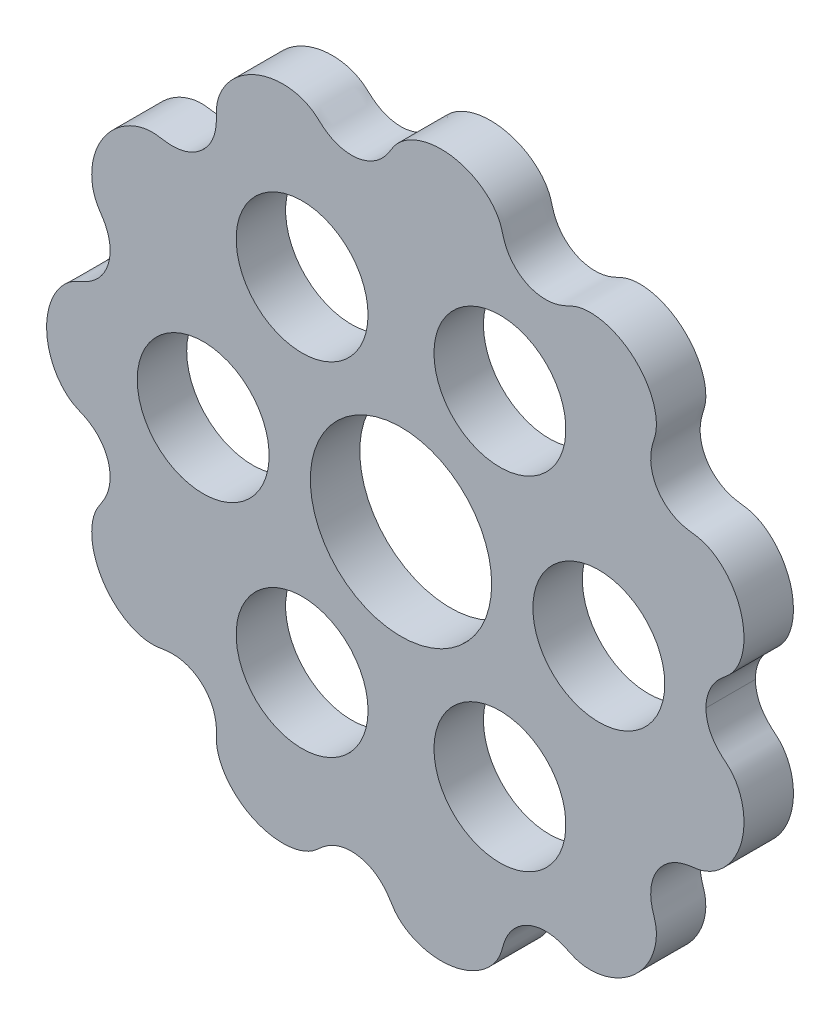
SolidWorks part; units mm, degrees
ref_plane "Front Plane" through (0, 0, 0) normal (0, 0, 1) x (1, 0, 0)
ref_plane "Top Plane" through (0, 0, 0) normal (0, 1, 0) x (1, 0, 0)
ref_plane "Right Plane" through (0, 0, 0) normal (1, 0, 0) x (0, 0, -1)
sketch "Sketch1" plane through (0, 0, 0) normal (0, 0, 1) x (1, 0, 0)
  circle A0 centre (0, 0) radius 50
  dimension "D1" = 100
extrude "Boss-Extrude1" add sketch "Sketch1" against normal blind 6
sketch "Sketch4" plane through (0, 0, 0) normal (0, 0, 1) x (1, 0, 0)
  line L1 (-43, 0) -> (37, 0) construction
  circle A0 centre (0, 0) radius 50
  circle A1 centre (0, 0) radius 50 construction
  spline S0 degree 4 poles (41.5851, 10.3346) (41.6199, 9.8835) (41.6243, 9.2034) (41.5317, 8.2988) (41.2403, 7.1964) (40.9372, 6.4519) (40.6006, 5.8458) (40.2846, 5.4003) (40.0318, 5.099) (39.7825, 4.8438) (39.5448, 4.6291) (39.2991, 4.4237) (39.054, 4.2176) (38.7552, 3.9511) (38.446, 3.6423) (38.1379, 3.2825) (37.8433, 2.8662) (37.6072, 2.4641) (37.4069, 2.043) (37.2646, 1.6607) (37.1673, 1.3249) (37.1028, 1.0413) (37.0614, 0.8113) (37.0342, 0.6103) (37.0173, 0.4389) (37.0076, 0.2873) (37.0024, 0.1621) (36.9997, 0.0436) (36.9998, -0.0533) (37.0029, -0.1805) (37.0092, -0.3185) (37.021, -0.4826) (37.0414, -0.6698) (37.0837, -0.9559) (37.1649, -1.3314) (37.2949, -1.7606) (37.4902, -2.2338) (37.7296, -2.6858) (38.0102, -3.1128) (38.3023, -3.4793) (38.5927, -3.7913) (38.8708, -4.0561) (39.128, -4.2811) (39.3908, -4.4995) (39.6509, -4.7212) (39.96, -5.0164) (40.2952, -5.4031) (40.633, -5.894) (40.9508, -6.4943) (41.2036, -7.1227) (41.4194, -7.8549) (41.5727, -8.6911) (41.636, -9.6259) (41.5806, -10.6475) (41.4043, -11.6601) (41.1093, -12.6496) (40.6979, -13.602) (40.1724, -14.5022) (39.4909, -15.3931) (38.7523, -16.1139) (37.9929, -16.6697) (37.2409, -17.0709) (36.6814, -17.2882) (36.1812, -17.4183) (35.7535, -17.4878) (35.4097, -17.5305) (35.0662, -17.5753) (34.7244, -17.6334) (33.9621, -17.799) (32.8171, -18.2368) (31.6914, -19.0898) (30.8224, -20.3839) (30.408, -21.5834) (30.2645, -22.5652) (30.2961, -23.3919) (30.4095, -24.0426) (30.5337, -24.523) (30.6289, -24.842) (30.7295, -25.1591) (30.8226, -25.4788) (30.9148, -25.8847) (30.9808, -26.383) (30.9944, -26.9717) (30.9331, -27.6434) (30.8023, -28.3074) (30.5866, -29.0299) (30.2677, -29.7983) (29.7091, -30.8112) (28.7943, -31.9885) (27.6691, -32.9783) (26.3797, -33.7385) (25.287, -34.1684) (24.4667, -34.3895) (23.7014, -34.5114) (23.0895, -34.5479) (22.5645, -34.5327) (22.0494, -34.4779) (21.6292, -34.3987) (21.2207, -34.2838) (20.8282, -34.133) (20.5223, -33.9937) (20.2197, -33.8474) (19.9143, -33.7068) (19.4515, -33.5146) (18.8164, -33.31) (17.9928, -33.1639) (16.9896, -33.1739) (15.7388, -33.4271) (14.34, -34.1197) (13.2844, -35.1853) (12.6832, -36.3498) (12.4167, -37.1715) (12.3007, -37.5873) (12.2097, -37.9202) (12.077, -38.3311) (11.8737, -38.8043) (11.5763, -39.3231) (11.0699, -40.0048) (10.2279, -40.8568) (8.9477, -41.7397) (7.1761, -42.4496) (5.3677, -42.7131) (3.8099, -42.6315) (2.6321, -42.3721) (1.8212, -42.0927) (1.1256, -41.7663) (0.541, -41.4194) (-0.0018, -41.0141) (-0.4313, -40.6073) (-0.7569, -40.2215) (-0.9962, -39.8786) (-1.1736, -39.5952) (-1.3489, -39.3105) (-1.532, -39.0307) (-1.8282, -38.6168) (-2.2737, -38.0967) (-2.9231, -37.5266) (-3.823, -37.0029) (-4.8035, -36.6676) (-5.8255, -36.5318) (-6.847, -36.5969) (-7.83, -36.8545) (-8.5941, -37.2186) (-9.1572, -37.5904) (-9.554, -37.904) (-9.8106, -38.1246) (-10.0615, -38.3513) (-10.3155, -38.5748) (-10.6482, -38.8362) (-11.0061, -39.0672) (-11.3852, -39.2662) (-11.8611, -39.4687) (-12.356, -39.6355) (-12.9486, -39.778) (-13.7162, -39.8842) (-14.5693, -39.9112) (-15.7506, -39.8147) (-17.2442, -39.4469) (-18.8902, -38.6799) (-20.382, -37.4935) (-21.3601, -36.2698) (-21.9217, -35.202) (-22.1788, -34.4781) (-22.3014, -33.9783) (-22.3596, -33.5951) (-22.3833, -33.3352) (-22.3952, -33.0746) (-22.3968, -32.8138) (-22.3902, -32.5096) (-22.3873, -32.1618) (-22.3978, -31.8141) (-22.4393, -31.2937) (-22.5601, -30.6065) (-22.9189, -29.5253) (-23.6399, -28.4298) (-24.6121, -27.5729) (-25.7462, -27.0054) (-26.6974, -26.7348) (-27.5181, -26.6568) (-28.1758, -26.6819) (-28.6667, -26.7394) (-28.9944, -26.7893) (-29.3213, -26.8434) (-29.6498, -26.8877) (-30.0633, -26.9174) (-30.5638, -26.9075) (-31.1457, -26.8334) (-31.7983, -26.674) (-32.4334, -26.4476) (-33.114, -26.1295) (-33.825, -25.7034) (-34.7425, -25.0061) (-35.7753, -23.9302) (-36.5936, -22.6707) (-37.1604, -21.2783) (-37.4266, -20.1279) (-37.5242, -19.283) (-37.5315, -18.511) (-37.4781, -17.9059) (-37.3867, -17.3936) (-37.2577, -16.8948) (-37.1182, -16.4917) (-36.9445, -16.1045) (-36.737, -15.7376) (-36.5542, -15.4544) (-36.3659, -15.175) (-36.1835, -14.8916) (-35.9275, -14.4575) (-35.6356, -13.852) (-35.3771, -13.0493) (-35.2517, -12.0445) (-35.3352, -10.8098) (-35.7196, -9.6388) (-36.3073, -8.7132) (-36.9724, -8.0325) (-37.4669, -7.6315) (-37.8668, -7.3655) (-38.2534, -7.1506) (-38.6177, -6.9754) (-38.9133, -6.8446) (-39.21, -6.7161) (-39.5023, -6.5777) (-39.8205, -6.4022) (-40.1575, -6.1807) (-40.6012, -5.8325) (-41.114, -5.3257) (-41.632, -4.6671) (-42.1172, -3.8458) (-42.4493, -3.0848) (-42.6697, -2.4088) (-42.7944, -1.8999) (-42.8599, -1.5689) (-42.9114, -1.2536) (-42.9441, -1.0039) (-42.9692, -0.7529) (-42.9848, -0.5312) (-42.9923, -0.3757) (-42.9975, -0.2143) (-43.0007, -0.0397) (-43.0003, 0.0847) (-42.9957, 0.293) (-42.9867, 0.4997) (-42.9737, 0.6941) (-42.9527, 0.9239) (-42.9207, 1.1877) (-42.8707, 1.5143) (-42.7946, 1.9043) (-42.6826, 2.3538) (-42.5224, 2.8587) (-42.3301, 3.3521) (-42.09, 3.8653) (-41.7941, 4.3914) (-41.4337, 4.9212) (-40.9994, 5.4418) (-40.511, 5.9138) (-40.0366, 6.2736) (-39.5966, 6.533) (-39.2118, 6.7155) (-38.8993, 6.8506) (-38.5101, 7.0233) (-37.9589, 7.3002) (-37.2793, 7.7414) (-36.7472, 8.2372) (-36.3985, 8.6664) (-36.2399, 8.8922) knots 0 0 0 0 0 0.010457 0.015686 0.020914 0.026295 0.028985 0.031675 0.033525 0.035376 0.037227 0.039077 0.040928 0.042779 0.04648 0.049171 0.051863 0.054554 0.057246 0.059937 0.061283 0.062628 0.063974 0.065319 0.065992 0.066665 0.067338 0.06801 0.06875 0.069491 0.070231 0.070971 0.072451 0.073931 0.076891 0.079851 0.082799 0.085748 0.088696 0.091645 0.09362 0.095594 0.097569 0.099544 0.101519 0.103494 0.107443 0.111351 0.115259 0.119167 0.123074 0.128973 0.134872 0.140771 0.146669 0.152679 0.158688 0.164698 0.170707 0.178536 0.182451 0.186366 0.19037 0.192373 0.194375 0.196377 0.198379 0.200382 0.202384 0.214412 0.226466 0.232173 0.237879 0.243576 0.249273 0.251196 0.253119 0.255043 0.256966 0.258889 0.260813 0.264659 0.268564 0.272469 0.276374 0.280279 0.285972 0.291665 0.30305 0.314568 0.320327 0.326086 0.330128 0.33417 0.338213 0.340234 0.342255 0.34614 0.348082 0.350025 0.351967 0.35391 0.355852 0.357795 0.36355 0.369305 0.37508 0.380855 0.392868 0.404851 0.408842 0.410837 0.412832 0.414827 0.416822 0.420812 0.424713 0.428614 0.436416 0.448392 0.460368 0.472309 0.47828 0.484251 0.488173 0.492095 0.496017 0.499939 0.503803 0.505735 0.507667 0.509599 0.511531 0.513463 0.515395 0.521361 0.527327 0.533319 0.539312 0.54516 0.551008 0.556835 0.562661 0.564616 0.566571 0.568526 0.57048 0.572435 0.57439 0.5783 0.580309 0.582319 0.586338 0.590358 0.594377 0.600204 0.606031 0.617686 0.629747 0.641809 0.649666 0.653594 0.657523 0.659533 0.661542 0.662547 0.663552 0.665562 0.667571 0.669581 0.671591 0.673601 0.679635 0.685669 0.697766 0.703453 0.709139 0.714817 0.720495 0.72241 0.724326 0.726241 0.728156 0.730071 0.731987 0.735817 0.739708 0.743598 0.747489 0.751379 0.757051 0.762723 0.774066 0.785679 0.791485 0.797291 0.801296 0.805301 0.809306 0.811308 0.813311 0.817206 0.819153 0.8211 0.823048 0.824995 0.826943 0.82889 0.834696 0.840502 0.846329 0.852156 0.863131 0.868612 0.871353 0.874093 0.87783 0.879699 0.881567 0.883436 0.885304 0.887173 0.889041 0.891829 0.894617 0.900194 0.905666 0.911137 0.916609 0.919345 0.922081 0.923244 0.924407 0.926733 0.927896 0.929058 0.92964 0.930221 0.931384 0.932914 0.933678 0.934443 0.935973 0.937502 0.939031 0.940561 0.94362 0.946678 0.949737 0.952796 0.955855 0.959766 0.963677 0.967588 0.971499 0.975435 0.977403 0.979372 0.98134 0.983308 0.987244 0.993622 1 1 1 1 1 construction
  spline S1 degree 4 poles (37, 0) (37, -0.0276) (37.0005, -0.0829) (37.0029, -0.1805) (37.0092, -0.3185) (37.021, -0.4826) (37.0414, -0.6698) (37.0837, -0.9559) (37.1649, -1.3314) (37.2949, -1.7606) (37.4902, -2.2338) (37.7296, -2.6858) (38.0102, -3.1128) (38.3023, -3.4793) (38.5927, -3.7913) (38.8708, -4.0561) (39.128, -4.2811) (39.3908, -4.4995) (39.6509, -4.7212) (39.96, -5.0164) (40.2952, -5.4031) (40.633, -5.894) (40.9508, -6.4943) (41.2036, -7.1227) (41.4194, -7.8549) (41.5727, -8.6911) (41.636, -9.6259) (41.5806, -10.6475) (41.4043, -11.6601) (41.1093, -12.6496) (40.6979, -13.602) (40.1724, -14.5022) (39.4909, -15.3931) (38.7523, -16.1139) (37.9929, -16.6697) (37.2409, -17.0709) (36.6814, -17.2882) (36.1812, -17.4183) (35.7535, -17.4878) (35.4097, -17.5305) (35.0662, -17.5753) (34.7244, -17.6334) (33.9621, -17.799) (32.8171, -18.2368) (31.6914, -19.0898) (30.8224, -20.3839) (30.408, -21.5834) (30.2645, -22.5652) (30.2961, -23.3919) (30.4095, -24.0426) (30.5337, -24.523) (30.6289, -24.842) (30.7295, -25.1591) (30.8226, -25.4788) (30.9148, -25.8847) (30.9808, -26.383) (30.9944, -26.9717) (30.9331, -27.6434) (30.8023, -28.3074) (30.5866, -29.0299) (30.2677, -29.7983) (29.7091, -30.8112) (28.7943, -31.9885) (27.6691, -32.9783) (26.3797, -33.7385) (25.287, -34.1684) (24.4667, -34.3895) (23.7014, -34.5114) (23.0895, -34.5479) (22.5645, -34.5327) (22.0494, -34.4779) (21.6292, -34.3987) (21.2207, -34.2838) (20.8282, -34.133) (20.5223, -33.9937) (20.2197, -33.8474) (19.9143, -33.7068) (19.4515, -33.5146) (18.8164, -33.31) (17.9928, -33.1639) (16.9896, -33.1739) (15.7388, -33.4271) (14.34, -34.1197) (13.2844, -35.1853) (12.6832, -36.3498) (12.4167, -37.1715) (12.3007, -37.5873) (12.2097, -37.9202) (12.077, -38.3311) (11.8737, -38.8043) (11.5763, -39.3231) (11.0699, -40.0048) (10.2279, -40.8568) (8.9477, -41.7397) (7.1761, -42.4496) (5.3677, -42.7131) (3.8099, -42.6315) (2.6321, -42.3721) (1.8212, -42.0927) (1.1256, -41.7663) (0.541, -41.4194) (-0.0018, -41.0141) (-0.4313, -40.6073) (-0.7569, -40.2215) (-0.9962, -39.8786) (-1.1736, -39.5952) (-1.3489, -39.3105) (-1.532, -39.0307) (-1.8282, -38.6168) (-2.2737, -38.0967) (-2.9231, -37.5266) (-3.823, -37.0029) (-4.8035, -36.6676) (-5.8255, -36.5318) (-6.847, -36.5969) (-7.83, -36.8545) (-8.5941, -37.2186) (-9.1572, -37.5904) (-9.554, -37.904) (-9.8106, -38.1246) (-10.0615, -38.3513) (-10.3155, -38.5748) (-10.6482, -38.8362) (-11.0061, -39.0672) (-11.3852, -39.2662) (-11.8611, -39.4687) (-12.356, -39.6355) (-12.9486, -39.778) (-13.7162, -39.8842) (-14.5693, -39.9112) (-15.7506, -39.8147) (-17.2442, -39.4469) (-18.8902, -38.6799) (-20.382, -37.4935) (-21.3601, -36.2698) (-21.9217, -35.202) (-22.1788, -34.4781) (-22.3014, -33.9783) (-22.3596, -33.5951) (-22.3833, -33.3352) (-22.3952, -33.0746) (-22.3968, -32.8138) (-22.3902, -32.5096) (-22.3873, -32.1618) (-22.3978, -31.8141) (-22.4393, -31.2937) (-22.5601, -30.6065) (-22.9189, -29.5253) (-23.6399, -28.4298) (-24.6121, -27.5729) (-25.7462, -27.0054) (-26.6974, -26.7348) (-27.5181, -26.6568) (-28.1758, -26.6819) (-28.6667, -26.7394) (-28.9944, -26.7893) (-29.3213, -26.8434) (-29.6498, -26.8877) (-30.0633, -26.9174) (-30.5638, -26.9075) (-31.1457, -26.8334) (-31.7983, -26.674) (-32.4334, -26.4476) (-33.114, -26.1295) (-33.825, -25.7034) (-34.7425, -25.0061) (-35.7753, -23.9302) (-36.5936, -22.6707) (-37.1604, -21.2783) (-37.4266, -20.1279) (-37.5242, -19.283) (-37.5315, -18.511) (-37.4781, -17.9059) (-37.3867, -17.3936) (-37.2577, -16.8948) (-37.1182, -16.4917) (-36.9445, -16.1045) (-36.737, -15.7376) (-36.5542, -15.4544) (-36.3659, -15.175) (-36.1835, -14.8916) (-35.9275, -14.4575) (-35.6356, -13.852) (-35.3771, -13.0493) (-35.2517, -12.0445) (-35.3352, -10.8098) (-35.7196, -9.6388) (-36.3073, -8.7132) (-36.9724, -8.0325) (-37.4669, -7.6315) (-37.8668, -7.3655) (-38.2534, -7.1506) (-38.6177, -6.9754) (-38.9133, -6.8446) (-39.21, -6.7161) (-39.5023, -6.5777) (-39.8205, -6.4022) (-40.1575, -6.1807) (-40.6012, -5.8325) (-41.114, -5.3257) (-41.632, -4.6671) (-42.1172, -3.8458) (-42.4493, -3.0848) (-42.6697, -2.4088) (-42.7944, -1.8999) (-42.8599, -1.5689) (-42.9114, -1.2536) (-42.9441, -1.0039) (-42.9692, -0.7529) (-42.9848, -0.5312) (-42.9923, -0.3757) (-42.9975, -0.2143) (-42.9994, -0.109) (-43, -0.0434) (-43, 0) knots 0.06801 0.06801 0.06801 0.06801 0.06801 0.06875 0.069491 0.070231 0.070971 0.072451 0.073931 0.076891 0.079851 0.082799 0.085748 0.088696 0.091645 0.09362 0.095594 0.097569 0.099544 0.101519 0.103494 0.107443 0.111351 0.115259 0.119167 0.123074 0.128973 0.134872 0.140771 0.146669 0.152679 0.158688 0.164698 0.170707 0.178536 0.182451 0.186366 0.19037 0.192373 0.194375 0.196377 0.198379 0.200382 0.202384 0.214412 0.226466 0.232173 0.237879 0.243576 0.249273 0.251196 0.253119 0.255043 0.256966 0.258889 0.260813 0.264659 0.268564 0.272469 0.276374 0.280279 0.285972 0.291665 0.30305 0.314568 0.320327 0.326086 0.330128 0.33417 0.338213 0.340234 0.342255 0.34614 0.348082 0.350025 0.351967 0.35391 0.355852 0.357795 0.36355 0.369305 0.37508 0.380855 0.392868 0.404851 0.408842 0.410837 0.412832 0.414827 0.416822 0.420812 0.424713 0.428614 0.436416 0.448392 0.460368 0.472309 0.47828 0.484251 0.488173 0.492095 0.496017 0.499939 0.503803 0.505735 0.507667 0.509599 0.511531 0.513463 0.515395 0.521361 0.527327 0.533319 0.539312 0.54516 0.551008 0.556835 0.562661 0.564616 0.566571 0.568526 0.57048 0.572435 0.57439 0.5783 0.580309 0.582319 0.586338 0.590358 0.594377 0.600204 0.606031 0.617686 0.629747 0.641809 0.649666 0.653594 0.657523 0.659533 0.661542 0.662547 0.663552 0.665562 0.667571 0.669581 0.671591 0.673601 0.679635 0.685669 0.697766 0.703453 0.709139 0.714817 0.720495 0.72241 0.724326 0.726241 0.728156 0.730071 0.731987 0.735817 0.739708 0.743598 0.747489 0.751379 0.757051 0.762723 0.774066 0.785679 0.791485 0.797291 0.801296 0.805301 0.809306 0.811308 0.813311 0.817206 0.819153 0.8211 0.823048 0.824995 0.826943 0.82889 0.834696 0.840502 0.846329 0.852156 0.863131 0.868612 0.871353 0.874093 0.87783 0.879699 0.881567 0.883436 0.885304 0.887173 0.889041 0.891829 0.894617 0.900194 0.905666 0.911137 0.916609 0.919345 0.922081 0.923244 0.924407 0.926733 0.927896 0.929058 0.92964 0.930221 0.931384 0.931384 0.931384 0.931384 0.931384
  spline S2 degree 4 poles (37, 0) (37, 0.0276) (37.0005, 0.0829) (37.0029, 0.1805) (37.0092, 0.3185) (37.021, 0.4826) (37.0414, 0.6698) (37.0837, 0.9559) (37.1649, 1.3314) (37.2949, 1.7606) (37.4902, 2.2338) (37.7296, 2.6858) (38.0102, 3.1128) (38.3023, 3.4793) (38.5927, 3.7913) (38.8708, 4.0561) (39.128, 4.2811) (39.3908, 4.4995) (39.6509, 4.7212) (39.96, 5.0164) (40.2952, 5.4031) (40.633, 5.894) (40.9508, 6.4943) (41.2036, 7.1227) (41.4194, 7.8549) (41.5727, 8.6911) (41.636, 9.6259) (41.5806, 10.6475) (41.4043, 11.6601) (41.1093, 12.6496) (40.6979, 13.602) (40.1724, 14.5022) (39.4909, 15.3931) (38.7523, 16.1139) (37.9929, 16.6697) (37.2409, 17.0709) (36.6814, 17.2882) (36.1812, 17.4183) (35.7535, 17.4878) (35.4097, 17.5305) (35.0662, 17.5753) (34.7244, 17.6334) (33.9621, 17.799) (32.8171, 18.2368) (31.6914, 19.0898) (30.8224, 20.3839) (30.408, 21.5834) (30.2645, 22.5652) (30.2961, 23.3919) (30.4095, 24.0426) (30.5337, 24.523) (30.6289, 24.842) (30.7295, 25.1591) (30.8226, 25.4788) (30.9148, 25.8847) (30.9808, 26.383) (30.9944, 26.9717) (30.9331, 27.6434) (30.8023, 28.3074) (30.5866, 29.0299) (30.2677, 29.7983) (29.7091, 30.8112) (28.7943, 31.9885) (27.6691, 32.9783) (26.3797, 33.7385) (25.287, 34.1684) (24.4667, 34.3895) (23.7014, 34.5114) (23.0895, 34.5479) (22.5645, 34.5327) (22.0494, 34.4779) (21.6292, 34.3987) (21.2207, 34.2838) (20.8282, 34.133) (20.5223, 33.9937) (20.2197, 33.8474) (19.9143, 33.7068) (19.4515, 33.5146) (18.8164, 33.31) (17.9928, 33.1639) (16.9896, 33.1739) (15.7388, 33.4271) (14.34, 34.1197) (13.2844, 35.1853) (12.6832, 36.3498) (12.4167, 37.1715) (12.3007, 37.5873) (12.2097, 37.9202) (12.077, 38.3311) (11.8737, 38.8043) (11.5763, 39.3231) (11.0699, 40.0048) (10.2279, 40.8568) (8.9477, 41.7397) (7.1761, 42.4496) (5.3677, 42.7131) (3.8099, 42.6315) (2.6321, 42.3721) (1.8212, 42.0927) (1.1256, 41.7663) (0.541, 41.4194) (-0.0018, 41.0141) (-0.4313, 40.6073) (-0.7569, 40.2215) (-0.9962, 39.8786) (-1.1736, 39.5952) (-1.3489, 39.3105) (-1.532, 39.0307) (-1.8282, 38.6168) (-2.2737, 38.0967) (-2.9231, 37.5266) (-3.823, 37.0029) (-4.8035, 36.6676) (-5.8255, 36.5318) (-6.847, 36.5969) (-7.83, 36.8545) (-8.5941, 37.2186) (-9.1572, 37.5904) (-9.554, 37.904) (-9.8106, 38.1246) (-10.0615, 38.3513) (-10.3155, 38.5748) (-10.6482, 38.8362) (-11.0061, 39.0672) (-11.3852, 39.2662) (-11.8611, 39.4687) (-12.356, 39.6355) (-12.9486, 39.778) (-13.7162, 39.8842) (-14.5693, 39.9112) (-15.7506, 39.8147) (-17.2442, 39.4469) (-18.8902, 38.6799) (-20.382, 37.4935) (-21.3601, 36.2698) (-21.9217, 35.202) (-22.1788, 34.4781) (-22.3014, 33.9783) (-22.3596, 33.5951) (-22.3833, 33.3352) (-22.3952, 33.0746) (-22.3968, 32.8138) (-22.3902, 32.5096) (-22.3873, 32.1618) (-22.3978, 31.8141) (-22.4393, 31.2937) (-22.5601, 30.6065) (-22.9189, 29.5253) (-23.6399, 28.4298) (-24.6121, 27.5729) (-25.7462, 27.0054) (-26.6974, 26.7348) (-27.5181, 26.6568) (-28.1758, 26.6819) (-28.6667, 26.7394) (-28.9944, 26.7893) (-29.3213, 26.8434) (-29.6498, 26.8877) (-30.0633, 26.9174) (-30.5638, 26.9075) (-31.1457, 26.8334) (-31.7983, 26.674) (-32.4334, 26.4476) (-33.114, 26.1295) (-33.825, 25.7034) (-34.7425, 25.0061) (-35.7753, 23.9302) (-36.5936, 22.6707) (-37.1604, 21.2783) (-37.4266, 20.1279) (-37.5242, 19.283) (-37.5315, 18.511) (-37.4781, 17.9059) (-37.3867, 17.3936) (-37.2577, 16.8948) (-37.1182, 16.4917) (-36.9445, 16.1045) (-36.737, 15.7376) (-36.5542, 15.4544) (-36.3659, 15.175) (-36.1835, 14.8916) (-35.9275, 14.4575) (-35.6356, 13.852) (-35.3771, 13.0493) (-35.2517, 12.0445) (-35.3352, 10.8098) (-35.7196, 9.6388) (-36.3073, 8.7132) (-36.9724, 8.0325) (-37.4669, 7.6315) (-37.8668, 7.3655) (-38.2534, 7.1506) (-38.6177, 6.9754) (-38.9133, 6.8446) (-39.21, 6.7161) (-39.5023, 6.5777) (-39.8205, 6.4022) (-40.1575, 6.1807) (-40.6012, 5.8325) (-41.114, 5.3257) (-41.632, 4.6671) (-42.1172, 3.8458) (-42.4493, 3.0848) (-42.6697, 2.4088) (-42.7944, 1.8999) (-42.8599, 1.5689) (-42.9114, 1.2536) (-42.9441, 1.0039) (-42.9692, 0.7529) (-42.9848, 0.5312) (-42.9923, 0.3757) (-42.9975, 0.2143) (-42.9994, 0.109) (-43, 0.0434) (-43, 0) knots 0.06801 0.06801 0.06801 0.06801 0.06801 0.06875 0.069491 0.070231 0.070971 0.072451 0.073931 0.076891 0.079851 0.082799 0.085748 0.088696 0.091645 0.09362 0.095594 0.097569 0.099544 0.101519 0.103494 0.107443 0.111351 0.115259 0.119167 0.123074 0.128973 0.134872 0.140771 0.146669 0.152679 0.158688 0.164698 0.170707 0.178536 0.182451 0.186366 0.19037 0.192373 0.194375 0.196377 0.198379 0.200382 0.202384 0.214412 0.226466 0.232173 0.237879 0.243576 0.249273 0.251196 0.253119 0.255043 0.256966 0.258889 0.260813 0.264659 0.268564 0.272469 0.276374 0.280279 0.285972 0.291665 0.30305 0.314568 0.320327 0.326086 0.330128 0.33417 0.338213 0.340234 0.342255 0.34614 0.348082 0.350025 0.351967 0.35391 0.355852 0.357795 0.36355 0.369305 0.37508 0.380855 0.392868 0.404851 0.408842 0.410837 0.412832 0.414827 0.416822 0.420812 0.424713 0.428614 0.436416 0.448392 0.460368 0.472309 0.47828 0.484251 0.488173 0.492095 0.496017 0.499939 0.503803 0.505735 0.507667 0.509599 0.511531 0.513463 0.515395 0.521361 0.527327 0.533319 0.539312 0.54516 0.551008 0.556835 0.562661 0.564616 0.566571 0.568526 0.57048 0.572435 0.57439 0.5783 0.580309 0.582319 0.586338 0.590358 0.594377 0.600204 0.606031 0.617686 0.629747 0.641809 0.649666 0.653594 0.657523 0.659533 0.661542 0.662547 0.663552 0.665562 0.667571 0.669581 0.671591 0.673601 0.679635 0.685669 0.697766 0.703453 0.709139 0.714817 0.720495 0.72241 0.724326 0.726241 0.728156 0.730071 0.731987 0.735817 0.739708 0.743598 0.747489 0.751379 0.757051 0.762723 0.774066 0.785679 0.791485 0.797291 0.801296 0.805301 0.809306 0.811308 0.813311 0.817206 0.819153 0.8211 0.823048 0.824995 0.826943 0.82889 0.834696 0.840502 0.846329 0.852156 0.863131 0.868612 0.871353 0.874093 0.87783 0.879699 0.881567 0.883436 0.885304 0.887173 0.889041 0.891829 0.894617 0.900194 0.905666 0.911137 0.916609 0.919345 0.922081 0.923244 0.924407 0.926733 0.927896 0.929058 0.92964 0.930221 0.931384 0.931384 0.931384 0.931384 0.931384
extrude "Cut-Extrude1" cut sketch "Sketch4" against normal through all
sketch "Sketch5" plane through (0, 0, 0) normal (0, 0, 1) x (1, 0, 0)
  circle A0 centre (0, 0) radius 11
  dimension "D1" = 22
extrude "Cut-Extrude2" cut sketch "Sketch5" against normal through all
sketch "Sketch6" plane through (0, 0, 0) normal (0, 0, 1) x (1, 0, 0)
  circle A0 centre (0, 0) radius 24 construction
  circle A1 centre (24, 0) radius 8
  point P5 (0, 20.5564)
  point P6 (23, 0)
  dimension "D1" = 16
  dimension "D2" = 48
extrude "Cut-Extrude3" cut sketch "Sketch6" against normal through all
pattern_circular "CirPattern1" count 6 over 360 about axis through (0, 0, 0) along (0, 0, 1) of "Cut-Extrude3"
equation "\"R\"= 45"
equation "\"Rr\"= 5"
equation "\"N\"= 12"
equation "\"E\"= 3"
equation "\"D1@Sketch1\"=2*\"R\"+10"
